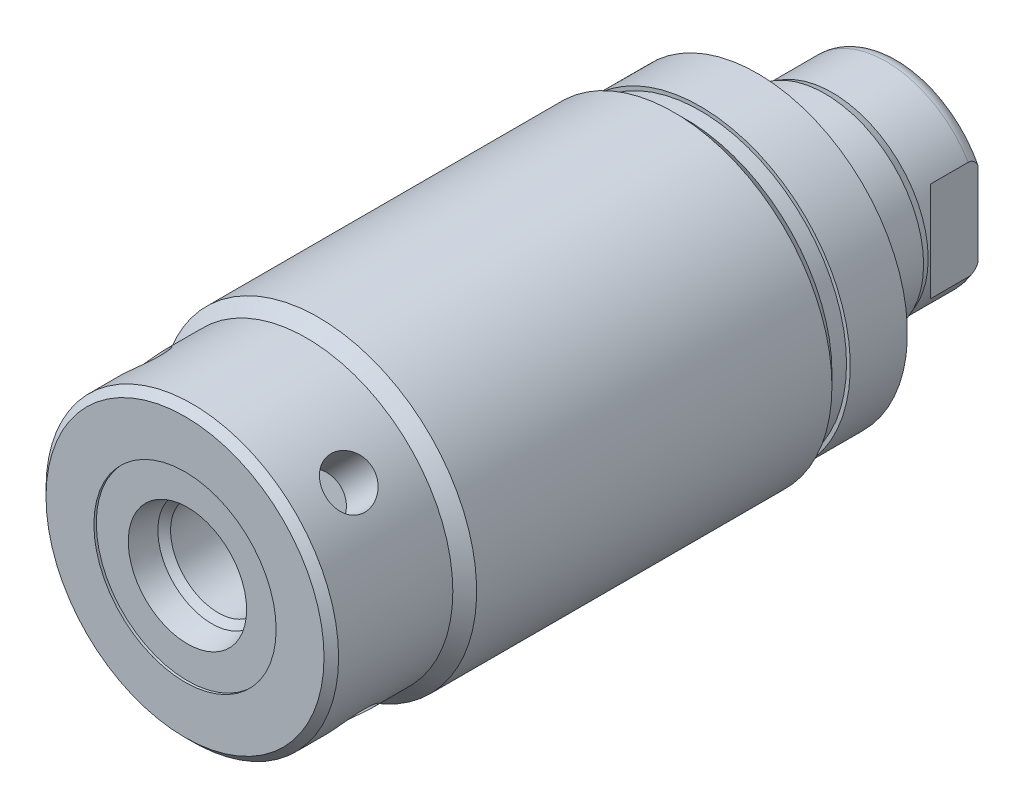
SolidWorks part; units mm, degrees
material "Alloy Steel"
ref_plane "Front Plane" through (0, 0, 0) normal (0, 0, 1) x (1, 0, 0)
ref_plane "Top Plane" through (0, 0, 0) normal (0, 1, 0) x (1, 0, 0)
ref_plane "Right Plane" through (0, 0, 0) normal (1, 0, 0) x (0, 0, -1)
ref_plane "Plane1" through (0, 0, 0) normal (0, 0, 1) x (1, 0, 0)
sketch "Sketch1" plane through (0, 0, 0) normal (0, 0, 1) x (1, 0, 0)
  circle A0 centre (0, 0) radius 16.5354
  dimension "D1" = 33.0708
extrude "Extrude1" add sketch "Sketch1" along normal blind 53.848
sketch "Sketch2" plane through (0, 0, 0) normal (0, 1, 0) x (1, 0, 0)
  line L0 (16.5354, -53.848) -> (16.5354, -39.9034)
  line L1 (16.5354, -39.9034) -> (15.2908, -41.148)
  line L2 (15.2908, -41.148) -> (15.2908, -53.848)
  line L3 (15.2908, -53.848) -> (16.5354, -53.848)
  line L4 (0, 0) -> (0, -24.4965) construction
  line L5 (-16.5354, -53.848) -> (16.5354, -53.848) construction
  line L6 (16.5354, -53.848) -> (16.5354, 0) construction
  dimension "D1" = 12.7
  dimension "D2" = 30.5816
  dimension "D3" = 45
revolve "Cut-Revolve1" cut sketch "Sketch2" angle 360 about L4
sketch "Sketch3" plane through (0, 0, 0) normal (0, 1, 0) x (1, 0, 0)
  line L0 (15.2908, 0) -> (15.2908, -1.524)
  line L1 (15.2908, -1.524) -> (16.5354, -2.7686)
  line L2 (16.5354, -2.7686) -> (16.5354, 0)
  line L3 (16.5354, 0) -> (15.2908, 0)
  line L4 (0, 0) -> (0, 3.0455) construction
  line L5 (15.2908, -53.848) -> (15.2908, -41.148) construction
  line L6 (16.5354, 0) -> (-16.5354, 0) construction
  line L7 (16.5354, -39.9034) -> (16.5354, 0) construction
  dimension "D1" = 45
  dimension "D2" = 1.524
revolve "Cut-Revolve2" cut sketch "Sketch3" angle 360 about L4
sketch "S2D0002" plane through (0, 0, 0) normal (0, 1, 0) x (1, 0, 0)
  line L0 (6.1849, -53.594) -> (9.525, -53.594)
  line L1 (6.1849, -53.594) -> (5.6423, -51.0413)
  line L2 (5.6423, -51.0413) -> (4.9784, -50.3774)
  line L3 (4.9784, -50.3774) -> (4.9784, -39.624)
  line L4 (4.9784, -39.624) -> (0, -39.624)
  line L5 (0, -39.624) -> (0, -53.848)
  line L6 (0, -14.6685) -> (0, 0.6985) construction
  line L8 (9.525, -53.594) -> (9.525, -53.848)
  line L9 (-15.2908, -53.848) -> (15.2908, -53.848) construction
  line L10 (9.525, -53.848) -> (0, -53.848)
  dimension "D1" = 19.05
  dimension "D2" = 9.9568
  dimension "D3" = 0.254
  dimension "D4" = 12.3698
  dimension "D5" = 12
  dimension "D6" = 45
  dimension "D7" = 2.5527
  dimension "D8" = 13.97
revolve "Cut-Revolve3" cut sketch "S2D0002" angle 360 about L6
chamfer "Chamfer1" distance 0.762 angle 45 1 edges at (-15.2908, 0, 53.848)
sketch "Sketch6" plane through (0, 0, 0) normal (0, 0, -1) x (-1, 0, 0)
  circle A0 centre (0, 0) radius 15.6845
  circle A1 centre (0, 0) radius 16.5354 construction
  dimension "D1" = 31.369
extrude "Extrude2" add sketch "Sketch6" along normal blind 5.969
sketch "Sketch7" plane through (0, 0, 0) normal (1, 0, 0) x (0, 0, -1)
  line L0 (5.969, 0) -> (5.969, -10.3187)
  line L1 (5.969, -10.3187) -> (20.447, -10.3187)
  line L2 (20.447, -10.3187) -> (20.447, 0)
  line L3 (20.447, 0) -> (5.969, 0)
  line L4 (0, 0) -> (9.7123, 0) construction
  line L5 (5.969, -15.6845) -> (5.969, 15.6845) construction
  dimension "D1" = 20.6375
  dimension "D2" = 14.478
revolve "Revolve1" add sketch "Sketch7" angle 360 about L4
sketch "S2D0001" plane through (0, 0, 0) normal (0, 1, 0) x (1, 0, 0)
  line L0 (3.2639, 18.5113) -> (3.2639, 3.8608)
  line L1 (3.2639, 3.8608) -> (0, 3.8608)
  line L2 (4.3815, 20.447) -> (0, 20.447)
  line L3 (0, 20.447) -> (0, 3.8608)
  line L4 (3.2639, 18.5113) -> (4.3815, 20.447)
  line L5 (0, -31.3084) -> (0, 2.765) construction
  line L6 (10.3187, 20.447) -> (-10.3187, 20.447) construction
  dimension "D1" = 8.763
  dimension "D2" = 30
  dimension "D3" = 16.5862
  dimension "D4" = 6.5278
revolve "Cut-Revolve5" cut sketch "S2D0001" angle 360 about L5
ref_plane "Plane8" through (0, 0, 0) normal (1, 0, 0) x (0, -1, 0)
sketch "Sketch9" plane through (0, 0, 0) normal (1, 0, 0) x (0, -1, 0)
  line L0 (-10.3187, 13.0302) -> (-10.033, 13.7922)
  line L1 (-10.033, 13.7922) -> (-10.033, 19.431)
  line L2 (0, 12.6594) -> (0, 20.8178) construction
  line L3 (10.3187, 20.447) -> (-10.3188, 20.447) construction
  line L4 (-9.6449, 20.447) -> (-10.3188, 20.447)
  line L5 (-10.3188, 20.447) -> (-10.3187, 13.0302)
  arc A0 (-9.6449, 20.447) -> (-10.033, 19.431) centre (-8.509, 19.431) ccw
  dimension "D1" = 1.524
  dimension "D2" = 1.016
  dimension "D3" = 20.066
  dimension "D4" = 0.762
  dimension "D5" = 7.4168
revolve "Cut-Revolve6" cut sketch "Sketch9" angle 360 about L2
sketch "Sketch13" plane through (0, 0, 0) normal (0, 1, 0) x (1, 0, 0)
  line L0 (8.5852, 20.447) -> (8.5852, 15.494)
  line L1 (8.5852, 15.494) -> (10.033, 14.0462)
  line L2 (-8.5852, 20.447) -> (-8.5852, 15.494)
  line L3 (-8.5852, 15.494) -> (-10.033, 14.0462)
  line L4 (9.6449, 20.447) -> (-9.6449, 20.447) construction
  line L5 (0, 13.7262) -> (0, 20.767) construction
  line L6 (10.033, 14.0462) -> (10.033, 20.447)
  line L8 (8.5852, 20.447) -> (10.033, 20.447)
  line L9 (10.033, 13.7922) -> (10.033, 19.431) construction
  line L10 (-10.033, 14.0462) -> (-10.033, 20.447)
  line L11 (-8.5852, 20.447) -> (-10.033, 20.447)
  dimension "D1" = 17.1704
  dimension "D2" = 135
  dimension "D3" = 4.953
extrude "Cut-Extrude4" cut sketch "Sketch13" against normal mid plane 39.685
ref_plane "Plane13" through (0, 0, 0) normal (0.7071, 0.7071, 0) x (0, 0, -1)
hole_wizard "Hole1" positions "3DSketch2" profile "Sketch14" legacy
sketch3d "3DSketch2"
  point P0 (-10.8122, 10.8122, 47.498)
  dimension "D1" = 6.35
sketch "Sketch14" plane through (-10.8122, 10.8122, 47.498) normal (0, 0, 1) x (-0.7071, -0.7071, 0)
  line L0 (0, 0) -> (0, 4.7498)
  line L1 (0, 4.7498) -> (2.5019, 4.7498)
  line L2 (2.5019, 4.7498) -> (2.5019, 0)
  line L3 (2.5019, 0) -> (0, 0)
  line L4 (0, 110) -> (0, -10) construction
  dimension "Diameter" = 5.0038
  dimension "Depth" = 4.7498
pattern_circular "CirPattern1" count 4 over 360 about axis through (0, 0, 0) along (0, 0, 1) of "Hole1"
